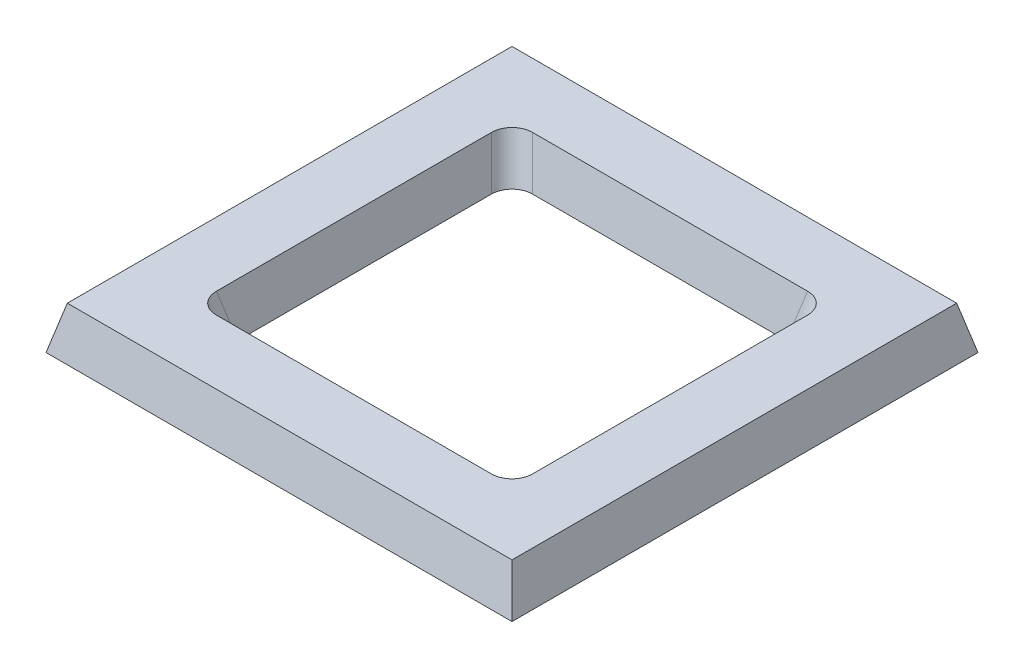
SolidWorks part; units mm, degrees
ref_plane "Front Plane" through (0, 0, 0) normal (0, 0, 1) x (1, 0, 0)
ref_plane "Top Plane" through (0, 0, 0) normal (0, 1, 0) x (1, 0, 0)
ref_plane "Right Plane" through (0, 0, 0) normal (1, 0, 0) x (0, 0, -1)
sketch "Sketch1" plane through (0, 0, 0) normal (0, 1, 0) x (1, 0, 0)
  line L1 (-34.5, -34.5) -> (34.5, -34.5)
  line L2 (-34.5, -34.5) -> (-34.5, 34.5)
  line L3 (-34.5, 34.5) -> (34.5, 34.5)
  line L4 (34.5, -34.5) -> (34.5, 34.5)
  line L5 (-34.5, -34.5) -> (34.5, 34.5) construction
  line L6 (-34.5, 34.5) -> (34.5, -34.5) construction
  point P0 (0, 0)
  dimension "D1" = 69
ref_plane "Plane1" through (0, 10, 0) normal (0, 1, 0) x (1, 0, 0)
extrude "Extrude-Thin1" add sketch "Sketch1" along normal blind 10 draft 14 thin
fillet "Fillet1" radius 5 4 edges at (35.7466, 5, 35.7466) (35.7466, 5, -35.7466) (-35.7466, 5, -35.7466) (-35.7466, 5, 35.7466)
sketch "Sketch3" plane through (0, 0, 0) normal (0, -1, 0) x (1, 0, 0)
  line L4 (54.5, -54.5) -> (54.5, 54.5)
  line L5 (54.5, 54.5) -> (-54.5, 54.5)
  line L6 (-54.5, 54.5) -> (-54.5, -54.5)
  line L7 (-54.5, -54.5) -> (54.5, -54.5)
  line L8 (54.5, -54.5) -> (54.5, 54.5)
  line L9 (54.5, 54.5) -> (-54.5, 54.5)
  line L10 (-54.5, 54.5) -> (-54.5, -54.5)
  line L11 (-54.5, -54.5) -> (54.5, -54.5)
  dimension "D1" = 0
ref_plane "Plane2" through (0, 0, 0) normal (1, 0, 0) x (0, 0, -1)
